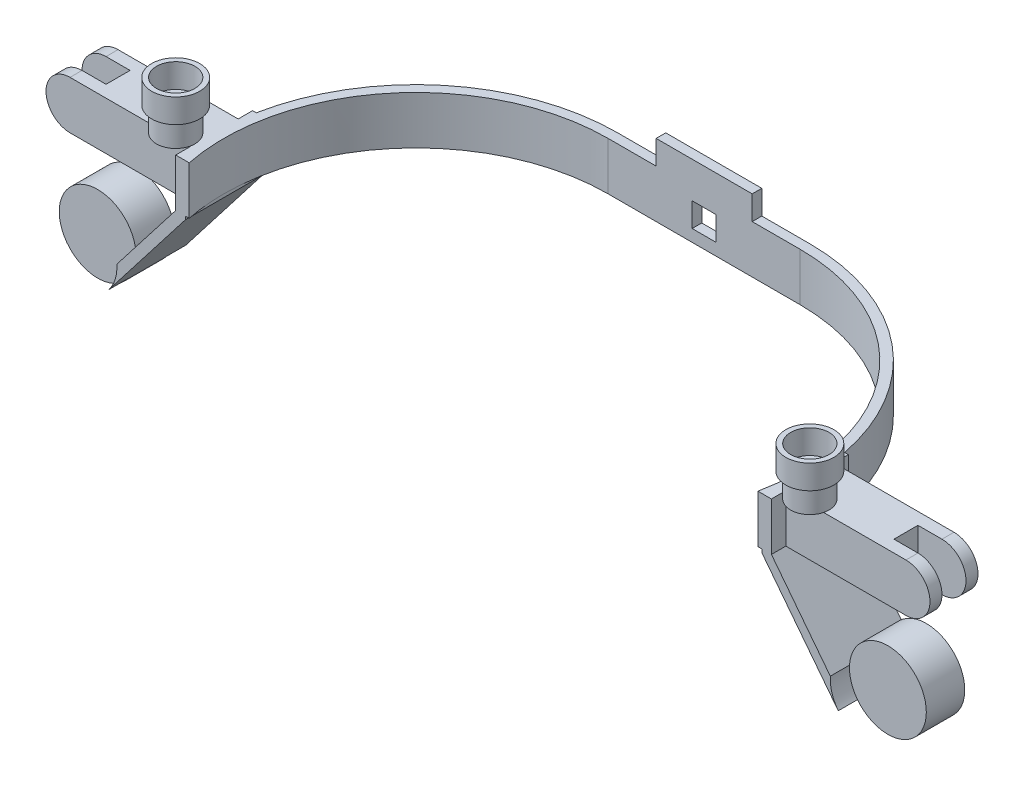
SolidWorks part; units mm, degrees
ref_plane "Front" through (0, 0, 0) normal (0, 0, 1) x (1, 0, 0)
ref_plane "Top" through (0, 0, 0) normal (0, 1, 0) x (1, 0, 0)
ref_plane "Right" through (0, 0, 0) normal (1, 0, 0) x (0, 0, -1)
sketch "草图2" plane through (0, 0, 0) normal (0, 1, 0) x (1, 0, 0)
  line L0 (-40, 0) -> (40, 0) construction
  line L1 (-40, 80) -> (40, 80)
  line L2 (-40, -80) -> (40, -80)
  line L3 (-40, 0) -> (40, 0) construction
  line L4 (-40, 84) -> (40, 84)
  line L5 (-40, -84) -> (40, -84)
  arc A0 (-40, 80) -> (-40, -80) centre (-40, 0) ccw
  arc A1 (40, -80) -> (40, 80) centre (40, 0) ccw
  arc A2 (-40, 84) -> (-40, -84) centre (-40, 0) ccw
  arc A3 (40, -84) -> (40, 84) centre (40, 0) ccw
  point P2 (0, 0)
  point P10 (0, 0)
extrude "凸台-拉伸1" add sketch "草图2" along normal blind 20
sketch "草图8" plane through (0, 20, 0) normal (0, 1, 0) x (1, 0, 0)
  line L0 (0, 0) -> (-175.2062, 0) construction
  line L1 (-124, 16) -> (-120, 16)
  line L2 (-124, 16) -> (-124, -16)
  line L3 (-124, -16) -> (-120, -16)
  line L4 (-120, 16) -> (-120, -16)
  dimension "D1" = 4
  dimension "D2" = 32
  dimension "D3" = 16
sketch "草图9" plane through (0, 0, 0) normal (0, 0, 1) x (1, 0, 0)
  line L0 (0, 0) -> (-176.3582, 0) construction
  line L1 (-155, -40) -> (155, -40) construction
  line L2 (0, 0) -> (0, -149.7853) construction
  line L3 (-124, 20) -> (-124, 0)
  line L4 (-124, 0) -> (-155, -40)
  point P11 (155, -40)
  dimension "D1" = 40
  dimension "D2" = 310
  dimension "D3" = 155
sketch "草图11" plane through (0, 20, 0) normal (0, 1, 0) x (1, 0, 0)
  line L0 (0, 0) -> (130.9327, 0) construction
  line L1 (0, 0) -> (0, 51.5924) construction
  line L3 (124, 16) -> (120, 16)
  line L4 (124, 16) -> (124, -16)
  line L5 (124, -16) -> (120, -16)
  line L6 (120, 16) -> (120, -16)
  dimension "D1" = 124
  dimension "D2" = 4
  dimension "D3" = 32
  dimension "D4" = 16
sketch "草图18" plane through (0, 0, -84) normal (0, 0, -1) x (-1, 0, 0)
  line L6 (-5, 5) -> (5, 5) construction
  line L7 (-5, 15) -> (5, 15)
  line L8 (-5, 15) -> (-5, 5)
  line L9 (-5, 5) -> (5, 5)
  line L10 (5, 15) -> (5, 5)
  dimension "D1" = 10
  dimension "D2" = 5
  dimension "D3" = 5
  dimension "D4" = 10
extrude "切除-拉伸6" cut sketch "草图18" against normal blind 10
sketch "草图20" plane through (0, 20, 0) normal (0, 1, 0) x (1, 0, 0)
  line L0 (0, 80) -> (0, 120.4936) construction
  line L1 (40, 80) -> (-40, 80) construction
  line L2 (40, 84) -> (-40, 84) construction
  line L3 (-20, 84) -> (20, 84)
  line L4 (-20, 84) -> (-20, 80)
  line L5 (-20, 80) -> (20, 80)
  line L6 (20, 84) -> (20, 80)
  dimension "D1" = 40
  dimension "D2" = 20
extrude "凸台-拉伸5" add sketch "草图20" along normal blind 10
sketch "草图22" plane through (0, 20, 0) normal (0, 1, 0) x (1, 0, 0)
  circle A0 centre (-132, -8) radius 8
  circle A1 centre (132, -8) radius 8
extrude "凸台-拉伸7" add sketch "草图22" along normal blind 10
sketch "草图23" plane through (0, 30, 0) normal (0, 1, 0) x (1, 0, 0)
  circle A0 centre (-132, -8) radius 8
  circle A1 centre (-132, -8) radius 10
  circle A2 centre (132, -8) radius 8
  circle A3 centre (132, -8) radius 10
extrude "凸台-拉伸8" add sketch "草图23" along normal blind 10 separate body
sweep "扫描1" add profiles "草图8" path "草图9"
sketch "草图24" plane through (0, 0, 0) normal (0, 0, 1) x (1, 0, 0)
  line L0 (-155, -40) -> (306.7115, -40) construction
  line L1 (124, 20) -> (124, 0)
  line L2 (124, 0) -> (155, -40)
  point P4 (155, -40)
sweep "扫描2" add profiles "草图11" path "草图24"
sketch "草图25" plane through (0, 20, 0) normal (0, 1, 0) x (1, 0, 0)
  line L1 (-122.4621, -16) -> (124.4416, -16)
  line L2 (-122.4621, -16) -> (-122.4621, -91.0614)
  line L3 (-122.4621, -91.0614) -> (124.4416, -91.0614)
  line L4 (124.4416, -16) -> (124.4416, -91.0614)
extrude "切除-拉伸7" cut sketch "草图25" against normal blind 30
sketch "草图26" plane through (-124, 0, 0) normal (-1, 0, 0) x (0, 0, 1)
  line L0 (0, 0) -> (0, 49.4965) construction
  line L1 (16, 0) -> (-16, 0) construction
  line L2 (-16, 20) -> (8, 20) construction
  line L3 (-10, 20) -> (10, 20)
  line L4 (-10, 20) -> (-10, 0)
  line L5 (-10, 0) -> (10, 0)
  line L6 (10, 20) -> (10, 0)
  dimension "D1" = 20
  dimension "D2" = 10
extrude "凸台-拉伸9" add sketch "草图26" along normal blind 60
sketch "草图28" plane through (124, 0, 0) normal (1, 0, 0) x (0, 0, -1)
  line L0 (0, 0) -> (0, 58.971) construction
  line L1 (-16, 20) -> (16, 20) construction
  line L2 (-10, 20) -> (10, 20)
  line L3 (-10, 20) -> (-10, 0)
  line L4 (-10, 0) -> (10, 0)
  line L5 (10, 20) -> (10, 0)
  line L6 (16, 0) -> (-16, 0) construction
  dimension "D1" = 20
  dimension "D2" = 10
extrude "凸台-拉伸10" add sketch "草图28" along normal blind 60
sketch "草图27" plane through (0, 0, 10) normal (0, 0, 1) x (1, 0, 0)
  line L0 (-184, 0) -> (-184, 20) construction
  line L2 (-174, 20) -> (-189, 20)
  line L4 (-174, 0) -> (-189, 0)
  line L5 (-189, 20) -> (-189, 0)
  line L6 (174, 20) -> (191.9619, 20)
  line L8 (174, 0) -> (191.9619, 0)
  line L9 (191.9619, 20) -> (191.9619, 0)
  arc A0 (-174, 20) -> (-174, 0) centre (-174, 10) ccw
  arc A1 (174, 0) -> (174, 20) centre (174, 10) ccw
  dimension "D1" = 10
  dimension "D2" = 5
extrude "切除-拉伸8" cut sketch "草图27" against normal blind 60
sketch "草图29" plane through (0, 0, 0) normal (0, 0, 1) x (1, 0, 0)
  line L1 (-184, 21.6126) -> (-164, 21.6126)
  line L2 (-184, 21.6126) -> (-184, -4.1111)
  line L3 (-184, -4.1111) -> (-164, -4.1111)
  line L4 (-164, 21.6126) -> (-164, -4.1111)
  line L5 (184, 23.8901) -> (164, 23.8901)
  line L6 (184, 23.8901) -> (184, -9.65)
  line L7 (184, -9.65) -> (164, -9.65)
  line L8 (164, 23.8901) -> (164, -9.65)
  dimension "D1" = 20
  dimension "D2" = 20
extrude "切除-拉伸9" cut sketch "草图29" against normal mid plane 10
sketch "草图30" plane through (0, 0, 0) normal (0, 0, 1) x (1, 0, 0)
  line L0 (-145.1358, -33.8018) -> (-154.1943, -45.4902) construction
  line L1 (-120, -1.3686) -> (-151.8383, -42.4503) construction
  line L2 (-151.8383, -42.4503) -> (-160.7166, -35.5696) construction
  line L3 (133.6536, -18.986) -> (155.5702, -47.2656) construction
  line L4 (120, -1.3686) -> (151.8383, -42.4503) construction
  line L5 (151.8383, -42.4503) -> (177.9979, -22.1767) construction
  circle A0 centre (-164.485, -32.6491) radius 16
  circle A1 centre (164.485, -32.6491) radius 16
extrude "切除-拉伸10" cut sketch "草图30" against normal through all both and the other way through all
sketch "草图31" plane through (0, 0, 0) normal (0, 0, 1) x (1, 0, 0)
  circle A0 centre (-164.485, -32.6491) radius 16
  circle A1 centre (164.485, -32.6491) radius 16
extrude "凸台-拉伸11" add sketch "草图31" along normal mid plane 16
